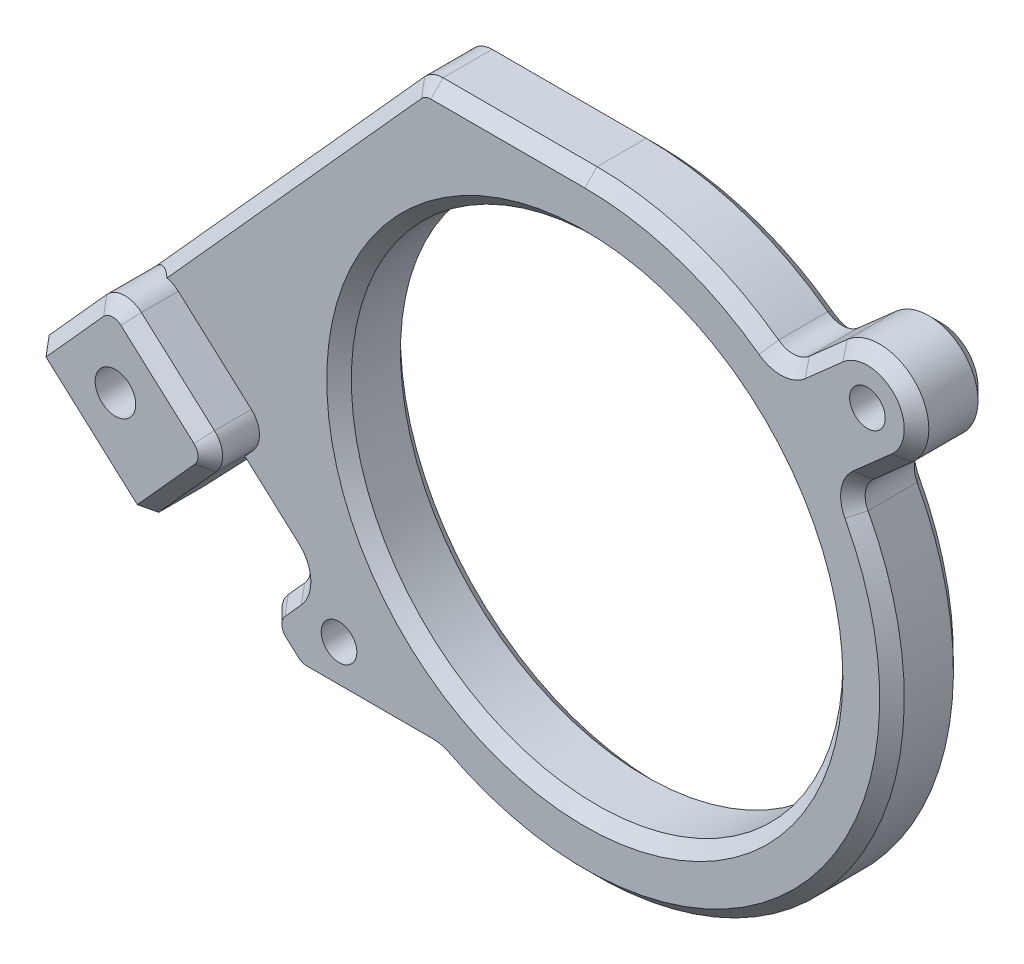
SolidWorks part; units mm, degrees
ref_plane "正面" through (0, 0, 0) normal (0, 0, 1) x (1, 0, 0)
ref_plane "平面" through (0, 0, 0) normal (0, 1, 0) x (1, 0, 0)
ref_plane "右側面" through (0, 0, 0) normal (1, 0, 0) x (0, 0, -1)
sketch "ｽｹｯﾁ1" plane through (0, 0, 0) normal (0, 0, 1) x (1, 0, 0)
  line L1 (30, -27.5) -> (-30, -27.5)
  line L2 (30, -27.5) -> (30, 27.5)
  line L3 (30, 27.5) -> (-30, 27.5)
  line L4 (-30, -27.5) -> (-30, 27.5)
  line L5 (30, -27.5) -> (-30, 27.5) construction
  line L6 (30, 27.5) -> (-30, -27.5) construction
  point P0 (0, 0)
  dimension "D1" = 55
  dimension "D2" = 60
extrude "ﾎﾞｽ - 押し出し1" add sketch "ｽｹｯﾁ1" along normal blind 6
sketch "ｽｹｯﾁ2" plane through (0, 0, 6) normal (0, 0, 1) x (1, 0, 0)
  line L0 (23, 20) -> (-20, -18)
  dimension "D1" = 18
  dimension "D2" = 20
  dimension "D3" = 43
  dimension "D4" = 38
hole_wizard "M4 すきま穴1" positions "ｽｹｯﾁ3" profile "ｽｹｯﾁ4" hole size "M4" standard "ISO"
sketch "ｽｹｯﾁ3" plane through (0, 0, 6) normal (0, 0, 1) x (1, 0, 0)
  point P0 (-20, -18)
  point P3 (23, 20)
sketch "ｽｹｯﾁ4" plane through (-20, -18, 6) normal (1, 0, 0) x (0, -1, 0)
  line L0 (0, 0) -> (0, 10)
  line L1 (0, 10) -> (1.45, 10)
  line L2 (1.45, 10) -> (1.45, 0)
  line L5 (1.45, 0) -> (0, 0)
  line L10 (0, 10) -> (-1.45, 10) construction
  line L11 (0, -6.35) -> (0, 107.95) construction
  dimension "穴の直径" = 2.9
  dimension "穴の深さ" = 10
  dimension "ﾄﾞﾘﾙ角度" = 180
sketch "ｽｹｯﾁ5" plane through (0, 0, 6) normal (0, 0, 1) x (1, 0, 0)
  circle A0 centre (0, 0) radius 20
  dimension "D1" = 40
extrude "ｶｯﾄ - 押し出し1" cut sketch "ｽｹｯﾁ5" against normal through all
sketch "ｽｹｯﾁ6" plane through (0, 0, 6) normal (0, 0, 1) x (1, 0, 0)
  line L0 (-20, -18) -> (23, 20) construction
  line L1 (23, 20) -> (-20, -18) construction
  line L2 (-22.6488, -15.0027) -> (20.3512, 22.9973)
  line L3 (-17.3512, -20.9973) -> (25.6488, 17.0027)
  line L8 (-30, 27.5) -> (-30, -27.5)
  line L9 (-30, -27.5) -> (30, -27.5)
  line L10 (30, -27.5) -> (30, 27.5)
  line L11 (30, 27.5) -> (-30, 27.5)
  line L12 (-30, 27.5) -> (-30, -27.5)
  line L13 (-30, -27.5) -> (30, -27.5)
  line L14 (30, -27.5) -> (30, 27.5)
  line L15 (30, 27.5) -> (-30, 27.5)
  circle A0 centre (0, 0) radius 20 construction
  circle A1 centre (0, 0) radius 20
  arc A2 (-22.6488, -15.0027) -> (-17.3512, -20.9973) centre (-20, -18) ccw
  arc A3 (25.6488, 17.0027) -> (20.3512, 22.9973) centre (23, 20) ccw
  circle A4 centre (0, 0) radius 25
  point P8 (1.5, 1)
  dimension "D2" = 50
  dimension "D1" = 8
  dimension "D3" = 0
extrude "ｶｯﾄ - 押し出し2" cut sketch "ｽｹｯﾁ6" against normal through all contours L13 L14 L15 L12 | A4 | A2 L3 A3 L2
sketch "ｽｹｯﾁ7" plane through (0, 0, 6) normal (0, 0, 1) x (1, 0, 0)
  line L0 (0, 25) -> (-20, 25)
  line L1 (-20, -22) -> (-21.5, -22)
  line L2 (-20, -22) -> (-20, 25)
  line L3 (-20, 25) -> (-21.5, 25)
  line L4 (-21.5, -22) -> (-21.5, 25)
  line L5 (-20, -22) -> (-11.8743, -22)
  line L8 (-21.0078, -13.5525) -> (-22.6488, -15.0027)
  line L9 (-17.3512, -20.9973) -> (-15.651, -19.4948)
  line L10 (21.2717, 13.1345) -> (25.6488, 17.0027)
  line L11 (20.3512, 22.9973) -> (16.0334, 19.1815)
  line L12 (-21.0078, -13.5525) -> (-22.6488, -15.0027)
  line L13 (-17.3512, -20.9973) -> (-15.651, -19.4948)
  line L14 (21.2717, 13.1345) -> (25.6488, 17.0027)
  line L15 (20.3512, 22.9973) -> (16.0334, 19.1815)
  arc A0 (-22.6488, -15.0027) -> (-17.3512, -20.9973) centre (-20, -18) ccw construction
  arc A5 (-22.6488, -15.0027) -> (-17.3512, -20.9973) centre (-20, -18) ccw
  arc A6 (-15.651, -19.4948) -> (21.2717, 13.1345) centre (0, 0) ccw
  arc A7 (25.6488, 17.0027) -> (20.3512, 22.9973) centre (23, 20) ccw
  arc A8 (16.0334, 19.1815) -> (-21.0078, -13.5525) centre (0, 0) ccw
  arc A9 (-22.6488, -15.0027) -> (-17.3512, -20.9973) centre (-20, -18) ccw
  arc A10 (-15.651, -19.4948) -> (21.2717, 13.1345) centre (0, 0) ccw
  arc A11 (25.6488, 17.0027) -> (20.3512, 22.9973) centre (23, 20) ccw
  arc A12 (16.0334, 19.1815) -> (-21.0078, -13.5525) centre (0, 0) ccw
  line M17 (-21.0078, -13.5525) -> (-22.6488, -15.0027)
  arc M18 (-22.6488, -15.0027) -> (-17.3512, -20.9973) centre (-20, -18) ccw
  line M19 (-17.3512, -20.9973) -> (-15.651, -19.4948)
  arc M20 (-15.651, -19.4948) -> (21.2717, 13.1345) centre (0, 0) ccw
  arc M24 (16.0334, 19.1815) -> (-21.0078, -13.5525) centre (0, 0) ccw
  dimension "D2" = 1.5
  dimension "D1" = 0
extrude "ﾎﾞｽ - 押し出し2" add sketch "ｽｹｯﾁ7" against normal up to surface (6 mm away) contours L4 L1 M18 M17 M24 | L4 L2 L3 M24 | L2 L0 M24 | L5 M18 M20 M19
sketch "ｽｹｯﾁ8" plane through (0, 0, 6) normal (0, 0, 1) x (1, 0, 0)
  line L0 (-21.5, 25) -> (-45.7174, -1.8961)
  line L1 (-45.7174, -1.8961) -> (-23.3898, -22)
  line L3 (-21.5, 12.7574) -> (-21.5, 25) construction
  line L4 (-20, -22) -> (-23.3898, -22)
  point P2 (-21.5, 25)
  point P3 (-45.0784, 1.4216)
  point P6 (-45.0784, 1.4216)
  dimension "D1" = 42
  dimension "D2" = 32
extrude "ﾎﾞｽ - 押し出し3" add sketch "ｽｹｯﾁ8" against normal up to surface (6 mm away) up to face at (-3.845, 3.3122, 0)
sketch "ｽｹｯﾁ9" plane through (0, 0, 0) normal (0, 0, -1) x (-1, 0, 0)
  line L0 (32.3408, -13.9405) -> (25.6495, -6.509)
  line L1 (23.3898, -22) -> (45.7174, -1.8961) construction
  line L2 (25.6495, -6.509) -> (39.0261, 5.5353)
  line L3 (45.7174, -1.8961) -> (21.5, 25) construction
  line M4 (23.3898, -22) -> (45.7174, -1.8961)
  line M5 (45.7174, -1.8961) -> (21.5, 25)
  dimension "D1" = 10
  dimension "D2" = 18
extrude "ﾎﾞｽ - 押し出し4" add sketch "ｽｹｯﾁ9" along normal blind 4 contours L2 L0 M4 M5
sketch "ｽｹｯﾁ10" plane through (0, 0, -4) normal (0, 0, -1) x (-1, 0, 0)
  line L0 (32.3408, -13.9405) -> (25.6495, -6.509) construction
  line L1 (25.6495, -6.509) -> (39.0261, 5.5353) construction
  line L2 (39.0261, 5.5353) -> (21.5, 25) construction
  line L3 (21.5, 25) -> (0, 25) construction
  line L4 (-16.0334, 19.1815) -> (-20.3512, 22.9973) construction
  line L5 (-25.6488, 17.0027) -> (-21.2717, 13.1345) construction
  line L6 (11.8743, -22) -> (23.3898, -22) construction
  line L8 (39.0261, 5.5353) -> (25.6495, -6.509) construction
  line L9 (25.6495, -6.509) -> (32.3408, -13.9405) construction
  line L10 (32.3408, -13.9405) -> (45.7174, -1.8961) construction
  line L11 (45.7174, -1.8961) -> (39.0261, 5.5353) construction
  line L12 (32.3408, -13.9405) -> (25.6495, -6.509)
  line L13 (34.5672, 1.5205) -> (39.0261, 5.5353)
  line L14 (39.0261, 5.5353) -> (21.5, 25)
  line L15 (21.5, 25) -> (13.4262, 25)
  line L16 (-16.0334, 19.1815) -> (-20.3512, 22.9973)
  line L17 (-25.6488, 17.0027) -> (-21.2717, 13.1345)
  line L18 (11.8743, -22) -> (23.3898, -22)
  line L20 (39.0261, 5.5353) -> (34.5672, 1.5205)
  line L21 (25.6495, -6.509) -> (32.3408, -13.9405)
  line L22 (41.2585, -5.9109) -> (45.7174, -1.8961)
  line L23 (45.7174, -1.8961) -> (39.0261, 5.5353)
  line L24 (41.2585, -5.9109) -> (13.4262, 25)
  line L29 (39.0261, 5.5353) -> (25.6495, -6.509)
  line L30 (25.6495, -6.509) -> (32.3408, -13.9405)
  line L31 (32.3408, -13.9405) -> (45.7174, -1.8961)
  line L32 (45.7174, -1.8961) -> (39.0261, 5.5353)
  line L33 (39.0261, 5.5353) -> (34.5672, 1.5205)
  line L34 (25.6495, -6.509) -> (32.3408, -13.9405)
  line L35 (32.3408, -13.9405) -> (45.7174, -1.8961)
  line L36 (45.7174, -1.8961) -> (39.0261, 5.5353)
  arc A0 (0, 25) -> (-16.0334, 19.1815) centre (0, 0) ccw construction
  arc A1 (-20.3512, 22.9973) -> (-25.6488, 17.0027) centre (-23, 20) ccw construction
  arc A2 (-21.2717, 13.1345) -> (11.8743, -22) centre (0, 0) ccw construction
  arc A3 (0, 25) -> (-16.0334, 19.1815) centre (0, 0) ccw
  arc A4 (-20.3512, 22.9973) -> (-25.6488, 17.0027) centre (-23, 20) ccw
  arc A5 (-21.2717, 13.1345) -> (11.8743, -22) centre (0, 0) ccw
  dimension "D1" = 6
  dimension "D2" = 0
extrude "ｶｯﾄ - 押し出し3" cut sketch "ｽｹｯﾁ10" against normal through all contours L14 L15 L24 L22 L23
sketch "ｽｹｯﾁ12" plane through (0, 0, 6) normal (0, 0, 1) x (1, 0, 0)
  line L0 (-41.2585, -5.9109) -> (-26.4793, -19.2181)
  line L1 (-41.2585, -5.9109) -> (-37.2437, -1.452)
  line L2 (-26.4793, -19.2181) -> (-22.4646, -14.7593)
  line L3 (-37.2437, -1.452) -> (-22.4646, -14.7593)
  line L4 (-41.2585, -5.9109) -> (-23.3898, -22) construction
  circle A0 centre (-20, -18) radius 1.45 construction
  dimension "D1" = 4
  dimension "D2" = 6
extrude "ｶｯﾄ - 押し出し4" cut sketch "ｽｹｯﾁ12" against normal blind 6
fillet "ﾌｨﾚｯﾄ1" radius 2 3 edges at (-25.6495, -6.509, -2) (-34.5672, 1.5205, -2) (-26.4793, -19.2181, 3)
sketch "ｽｹｯﾁ13" plane through (0, 0, 0) normal (0, 0, 1) x (1, 0, 0)
  line L4 (-32.3408, -13.9405) -> (-28.326, -9.4816)
  line L5 (-28.326, -9.4816) -> (-37.2437, -1.452)
  line L6 (-37.2437, -1.452) -> (-41.2585, -5.9109)
  line L7 (-41.2585, -5.9109) -> (-32.3408, -13.9405)
  line L8 (-32.3408, -13.9405) -> (-28.326, -9.4816)
  line L9 (-28.326, -9.4816) -> (-37.2437, -1.452)
  line L10 (-37.2437, -1.452) -> (-41.2585, -5.9109)
  line L11 (-41.2585, -5.9109) -> (-32.3408, -13.9405)
  dimension "D1" = 0
extrude "ﾎﾞｽ - 押し出し5" add sketch "ｽｹｯﾁ13" along normal blind 6
chamfer "面取り2" distance 5 angle 45 1 edges at (-36.7996, -9.9257, 6)
fillet "ﾌｨﾚｯﾄ4" radius 2 8 edges at (-23.3898, -22, 3) (-13.4262, 25, 3) (-22.4646, -14.7593, 3) (-33.454, -6.21, 6) (-36.7996, -9.9257, 1) (21.2717, 13.1345, 3) (16.0334, 19.1815, 3) (-11.8743, -22, 3)
chamfer "面取り3" distance 1 angle 45 53 edges at (-29.6643, -10.9679, -4) (-26.4768, -6.5524, -4) (-38.582, -2.9383, -4) (-30.1083, -2.4942, -4) (-34.5239, 0.6932, -4) (-36.7996, -9.9257, -4) (20, 0, 0) (20, 0, 6) (-24.9638, 12.1863, 0) (-26.1384, -11.4513, 0) (-26.1384, -11.4513, 6) (-13.3492, 24.8271, 6) (-13.3492, 24.8271, 0) (-23.2919, -14.8026, 0) (-23.2919, -14.8026, 6) (-6.2679, 25, 0) (-6.2679, 25, 6) (-24.472, -16.9887, 6) (-24.472, -16.9887, 0) (7.7717, 23.7613, 6) (7.7717, 23.7613, 0) (-25.6521, -19.1748, 0) (-25.6521, -19.1748, 6) (16.0467, 19.7836, 6) (16.0467, 19.7836, 0) (-24.4767, -21.0213, 0) (18.8154, 21.6401, 0) (18.8154, 21.6401, 6) (-23.3388, -21.8672, 0) (-23.3388, -21.8672, 6) (25.9973, 22.6488, 6) (25.9973, 22.6488, 0) (-17.4957, -22, 6) (-17.4957, -22, 0) (24.0713, 15.6086, 6) (24.0713, 15.6086, 0) (-11.8979, -22.0563, 0) (-11.8979, -22.0563, 6) (21.8499, 13.0707, 6) (21.8499, 13.0707, 0) (17.8053, -17.5491, 0) (17.8053, -17.5491, 6) (-24.4767, -21.0213, 6) (-41.2585, -5.9109, -1.9142) (-25.6903, 11.3794, 6) (-41.1566, -5.7978, 0.9369) (-37.8707, -2.1483, 5.8478) (-39.5857, -4.0531, 3.5) (-28.3834, -9.5454, 6) (-32.3408, -13.9405, -1.9142) (-28.9529, -10.1779, 5.8478) (-32.2389, -13.8273, 0.9369) (-30.668, -12.0826, 3.5)
sketch "ｽｹｯﾁ14" plane through (0, 0, 6) normal (0, 0, 1) x (1, 0, 0)
  line L0 (-32.7933, -3.9817) -> (-34.1971, -5.5408)
  line L11 (-36.6154, -2.2487) -> (-29.1839, -8.94)
  line L12 (-28.4, -8.0693) -> (-23.2817, -12.6779)
  line L14 (-28.4, -8.0693) -> (-23.2817, -12.6779)
  line L16 (-23.0597, -16.9147) -> (-24.3979, -18.401)
  line L18 (-23.0597, -16.9147) -> (-24.3979, -18.401)
  line L19 (-24.3239, -19.8133) -> (-23.2912, -20.7431)
  line L21 (-36.6154, -2.2487) -> (-29.1839, -8.94)
  line L30 (-24.3239, -19.8133) -> (-23.2912, -20.7431)
  line L50 (-33.0839, -13.2714) -> (-40.5154, -6.58) construction
  line L87 (-13.2789, 23.6691) -> (-36.6154, -2.2487)
  line L88 (-13.2789, 23.6691) -> (-36.6154, -2.2487)
  line L89 (-29.1839, -8.94) -> (-28.4, -8.0693)
  line L90 (-29.1839, -8.94) -> (-28.4, -8.0693)
  line L97 (-22.622, -21) -> (-12.3693, -21)
  line L98 (-22.622, -21) -> (-12.3693, -21)
  line L99 (21.8316, 14.9639) -> (24.9866, 17.752)
  line L100 (21.8316, 14.9639) -> (24.9866, 17.752)
  line L101 (21.0134, 22.248) -> (17.9417, 19.5335)
  line L102 (21.0134, 22.248) -> (17.9417, 19.5335)
  line L103 (0, 24) -> (-12.5357, 24)
  line L104 (0, 24) -> (-12.5357, 24)
  arc A9 (-23.0597, -16.9147) -> (-23.2817, -12.6779) centre (-25.2891, -14.9073) ccw
  arc A11 (-23.0597, -16.9147) -> (-23.2817, -12.6779) centre (-25.2891, -14.9073) ccw
  arc A14 (-24.3979, -18.401) -> (-24.3239, -19.8133) centre (-23.6548, -19.0701) ccw
  arc A15 (-24.3979, -18.401) -> (-24.3239, -19.8133) centre (-23.6548, -19.0701) ccw
  arc A16 (-23.2912, -20.7431) -> (-22.622, -21) centre (-22.622, -20) ccw
  arc A17 (-23.2912, -20.7431) -> (-22.622, -21) centre (-22.622, -20) ccw
  arc A94 (-12.5357, 24) -> (-13.2789, 23.6691) centre (-12.5357, 23) ccw
  arc A95 (-12.5357, 24) -> (-13.2789, 23.6691) centre (-12.5357, 23) ccw
  arc A100 (-10.9949, -21.3333) -> (-12.3693, -21) centre (-12.3693, -24) ccw
  arc A101 (-10.9949, -21.3333) -> (-12.3693, -21) centre (-12.3693, -24) ccw
  arc A102 (-10.9949, -21.3333) -> (21.1717, 11.303) centre (0, 0) ccw
  arc A103 (-10.9949, -21.3333) -> (21.1717, 11.303) centre (0, 0) ccw
  arc A104 (21.8316, 14.9639) -> (21.1717, 11.303) centre (23.8182, 12.7159) ccw
  arc A105 (21.8316, 14.9639) -> (21.1717, 11.303) centre (23.8182, 12.7159) ccw
  arc A106 (24.9866, 17.752) -> (21.0134, 22.248) centre (23, 20) ccw
  arc A107 (24.9866, 17.752) -> (21.0134, 22.248) centre (23, 20) ccw
  arc A108 (14.1824, 19.3613) -> (17.9417, 19.5335) centre (15.9552, 21.7815) ccw
  arc A109 (14.1824, 19.3613) -> (17.9417, 19.5335) centre (15.9552, 21.7815) ccw
  arc A110 (14.1824, 19.3613) -> (0, 24) centre (0, 0) ccw
  arc A111 (14.1824, 19.3613) -> (0, 24) centre (0, 0) ccw
  point P5 (0, 0)
  dimension "D2" = 5
  dimension "D3" = 5
  dimension "D1" = 0
hole_wizard "M3 六角穴付き頭ねじ用座ぐり穴2" positions "ｽｹｯﾁ19" profile "ｽｹｯﾁ20" counterbore size "M3" standard "ISO"
sketch "ｽｹｯﾁ19" plane through (0, 0, 6) normal (0, 0, 1) x (1, 0, 0)
  point P0 (-34.1971, -5.5408)
sketch "ｽｹｯﾁ20" plane through (-34.1971, -5.5408, 6) normal (1, 0, 0) x (0, -1, 0)
  line L0 (0, 0) -> (0, 10.9914)
  line L1 (0, 10.9914) -> (1.65, 10)
  line L2 (1.65, 10) -> (1.65, 3.4)
  line L3 (1.65, 3.4) -> (3.25, 3.4)
  line L4 (3.25, 3.4) -> (3.25, 0)
  line L5 (3.25, 0) -> (0, 0)
  line L10 (0, 10.9914) -> (-1.65, 10) construction
  line L11 (0, -6.35) -> (0, 107.95) construction
  dimension "穴の直径" = 3.3
  dimension "穴の深さ" = 10
  dimension "座ぐり穴の直径" = 6.5
  dimension "座ぐり穴の深さ" = 3.4
  dimension "ﾄﾞﾘﾙ角度" = 118
mirror "ﾐﾗｰ1" about plane through (0, 0, -4) normal (0, 0, -1) of bodies 112
delete or keep bodies "ﾎﾞﾃﾞｨ-削除/保持1" type delete bodies bodies 112
